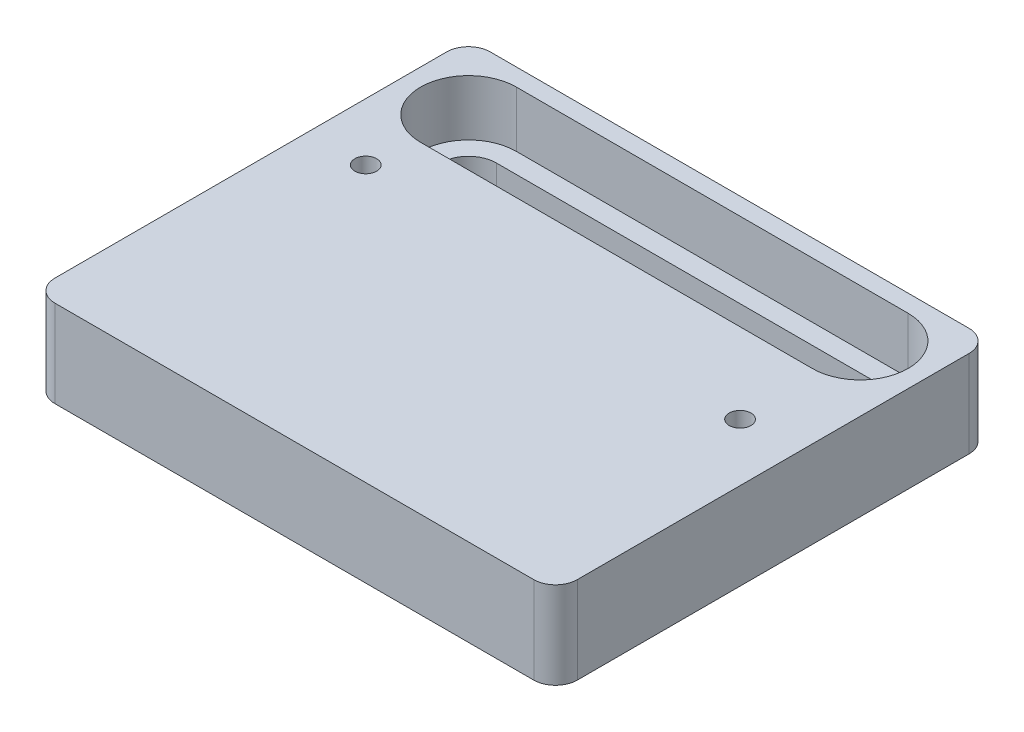
SolidWorks part; units mm, degrees
ref_plane "Front Plane" through (0, 0, 0) normal (0, 0, 1) x (1, 0, 0)
ref_plane "Top Plane" through (0, 0, 0) normal (0, 1, 0) x (1, 0, 0)
ref_plane "Right Plane" through (0, 0, 0) normal (1, 0, 0) x (0, 0, -1)
sketch "Sketch1" plane through (0, 0, 0) normal (0, 1, 0) x (1, 0, 0)
  line L1 (-30, 25) -> (30, 25)
  line L2 (-30, 25) -> (-30, -25)
  line L3 (-30, -25) -> (30, -25)
  line L4 (30, 25) -> (30, -25)
  line L5 (-30, 25) -> (30, -25) construction
  line L6 (-30, -25) -> (30, 25) construction
  point P0 (0, 0)
  dimension "D1" = 60
  dimension "D2" = 50
extrude "Boss-Extrude1" add sketch "Sketch1" along normal blind 10
sketch "Sketch2" plane through (0, 10, 0) normal (0, 1, 0) x (1, 0, 0)
  line L0 (0, 9.2) -> (0, -21) construction
  line L1 (28.25, -21) -> (-28.25, -21) construction
  line L2 (28.25, -21) -> (28.25, 9.2) construction
  line L3 (28.25, 9.2) -> (-28.25, 9.2) construction
  line L4 (-28.25, -21) -> (-28.25, 9.2) construction
  line L5 (28.25, -21) -> (-28.25, 9.2) construction
  line L6 (28.25, 9.2) -> (-28.25, -21) construction
  line L7 (0, -21) -> (0, -25) construction
  line L8 (-30, -25) -> (30, -25) construction
  point P0 (0, -5.9)
  point P5 (-23.4, 6.6)
  point P8 (23.4, 2.8)
  dimension "D1" = 30.2
  dimension "D2" = 56.5
  dimension "D3" = 23.4
  dimension "D4" = 23.4
  dimension "D5" = 23.8
  dimension "D6" = 27.6
  dimension "D7" = 4
hole_wizard "M3 Tapped Hole1" positions "Sketch3" profile "Sketch4" tap size "M3" standard "ISO" end condition up to next
sketch "Sketch3" plane through (0, 10, 0) normal (0, 1, 0) x (1, 0, 0)
  point P0 (-23.4, 6.6)
  point P3 (23.4, 2.8)
sketch "Sketch4" plane through (-23.4, 10, -6.6) normal (1, 0, 0) x (0, 0, 1)
  line L0 (0, 0) -> (0, 10)
  line L1 (0, 10) -> (1.25, 10)
  line L2 (1.25, 10) -> (1.25, 0)
  line L5 (1.25, 0) -> (0, 0)
  line L11 (0, -6.35) -> (0, 107.95) construction
  dimension "Thread Major Dia." = 2.5
  dimension "Thru Tap Drill Depth" = 10
sketch "Sketch7" plane through (0, 10, 0) normal (0, 1, 0) x (1, 0, 0)
  line L0 (-22.5, 17.5) -> (22.5, 17.5) construction
  line L1 (-22.5, 23) -> (22.5, 23)
  line L2 (-22.5, 12) -> (22.5, 12)
  line L3 (0, 25) -> (0, 17.5) construction
  line L4 (30, 25) -> (-30, 25) construction
  arc A0 (-22.5, 23) -> (-22.5, 12) centre (-22.5, 17.5) ccw
  arc A1 (22.5, 12) -> (22.5, 23) centre (22.5, 17.5) ccw
  point P2 (0, 17.5)
  point P7 (0, 14.427)
  point P12 (0, -32.1169)
  point P13 (0, -31.6515)
  dimension "D1" = 45
  dimension "D2" = 11
  dimension "D3" = 2
extrude "Cut-Extrude1" cut sketch "Sketch7" against normal blind 6.4
sketch "Sketch8" plane through (0, 3.6, 0) normal (0, 1, 0) x (1, 0, 0)
  line L0 (-22.5, 17.5) -> (22.5, 17.5) construction
  line L1 (-22.5, 20.7) -> (22.5, 20.7)
  line L2 (-22.5, 14.3) -> (22.5, 14.3)
  arc A0 (-22.5, 20.7) -> (-22.5, 14.3) centre (-22.5, 17.5) ccw
  arc A1 (22.5, 14.3) -> (22.5, 20.7) centre (22.5, 17.5) ccw
  point P4 (0, 17.5)
  dimension "D1" = 6.4
extrude "Cut-Extrude2" cut sketch "Sketch8" against normal through all
fillet "Fillet1" radius 2.5 4 edges at (-30, 5, -25) (-30, 5, 25) (30, 5, -25) (30, 5, 25)
